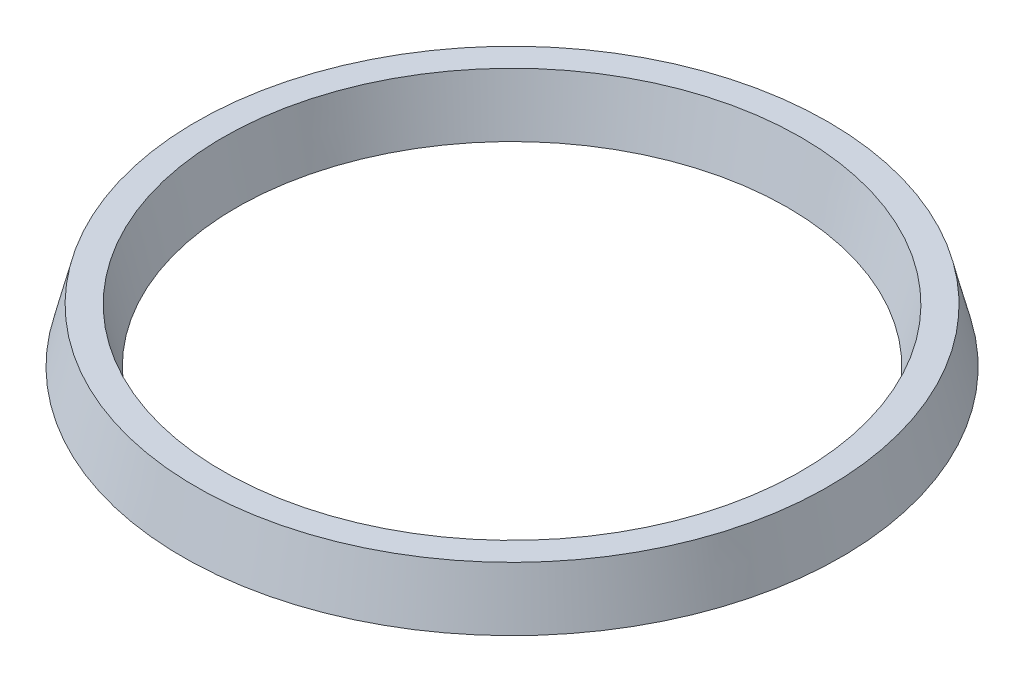
SolidWorks part; units mm, degrees
ref_plane "Front Plane" through (0, 0, 0) normal (0, 0, 1) x (1, 0, 0)
ref_plane "Top Plane" through (0, 0, 0) normal (0, 1, 0) x (1, 0, 0)
ref_plane "Right Plane" through (0, 0, 0) normal (1, 0, 0) x (0, 0, -1)
sketch "Sketch1" plane through (0, 0, 0) normal (0, 0, 1) x (1, 0, 0)
  line L0 (0, 15.3955) -> (0, 0) construction
  line L1 (0, 0) -> (-67.31, 0) construction
  line L2 (-67.31, 0) -> (-67.31, 22.5826) construction
  line L3 (3, 6) -> (-3, 6)
  line L4 (-3, 6) -> (-6, -6)
  line L5 (-6, -6) -> (-3, -6)
  line L6 (-3, -6) -> (-1.8638, -1.4552)
  line L8 (1.8638, -1.4552) -> (3, -6)
  line L9 (3, -6) -> (6, -6)
  line L10 (6, -6) -> (3, 6)
  arc A1 (-1.8638, -1.4552) -> (1.8638, -1.4552) centre (0, -1.9212) cw
  point P10 (-1.8917, -1.5667)
  point P14 (1.8907, -1.5667)
  dimension "D1" = 6
  dimension "D2" = 12
  dimension "D3" = 3
  dimension "D4" = 12
  dimension "D5" = 6
  dimension "D6" = 6
  dimension "D7" = 3
  dimension "D8" = 67.31
revolve "Revolve1" add sketch "Sketch1" angle 360 about L2
